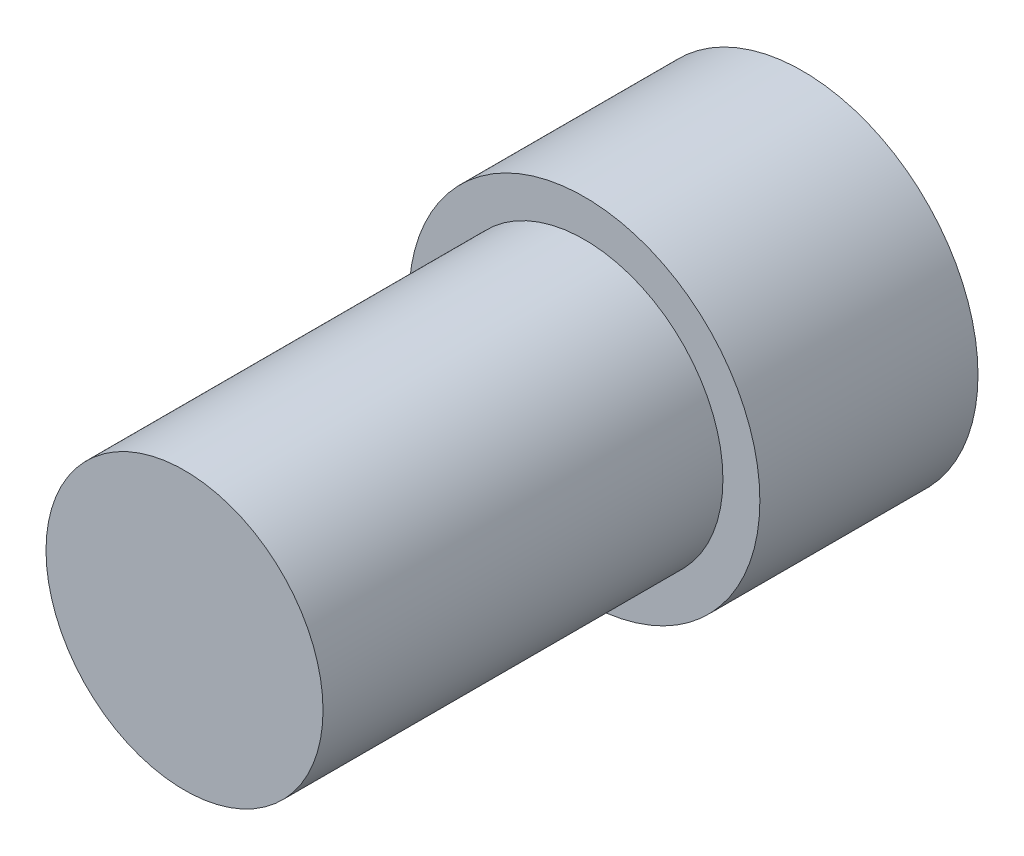
SolidWorks part; units mm, degrees
ref_plane "Front Plane" through (0, 0, 0) normal (0, 0, 1) x (1, 0, 0)
ref_plane "Top Plane" through (0, 0, 0) normal (0, 1, 0) x (1, 0, 0)
ref_plane "Right Plane" through (0, 0, 0) normal (1, 0, 0) x (0, 0, -1)
sketch "Sketch2" plane through (0, 0, 0) normal (0, 0, 1) x (1, 0, 0)
  circle A0 centre (0, 0) radius 4.826
  dimension "D1" = 9.652
extrude "Boss-Extrude1" add sketch "Sketch2" along normal blind 6
sketch "Sketch4" plane through (0, 0, 6) normal (0, 0, 1) x (1, 0, 0)
  circle A0 centre (0, 0) radius 3.81
  circle A1 centre (0, 0) radius 4.826 construction
  dimension "D1" = 7.62
extrude "Boss-Extrude2" add sketch "Sketch4" along normal blind 11
